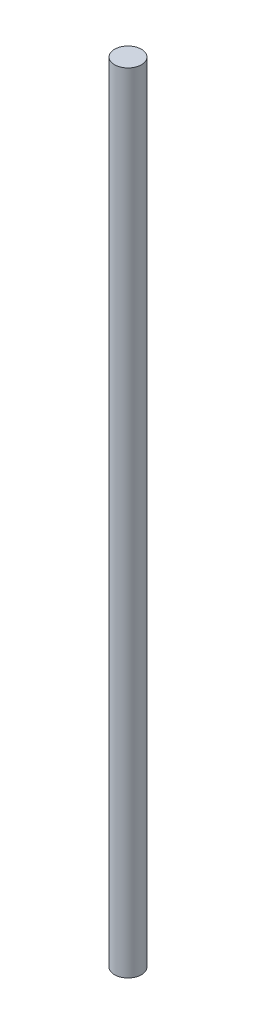
SolidWorks part; units mm, degrees
ref_plane "Front Plane" through (0, 0, 0) normal (0, 0, 1) x (1, 0, 0)
ref_plane "Top Plane" through (0, 0, 0) normal (0, 1, 0) x (1, 0, 0)
ref_plane "Right Plane" through (0, 0, 0) normal (1, 0, 0) x (0, 0, -1)
sketch "Sketch1" plane through (0, 0, 0) normal (0, 1, 0) x (1, 0, 0)
  circle A0 centre (0, 0) radius 9.525
  dimension "D1" = 19.05
extrude "Boss-Extrude1" add sketch "Sketch1" along normal blind 558.8
